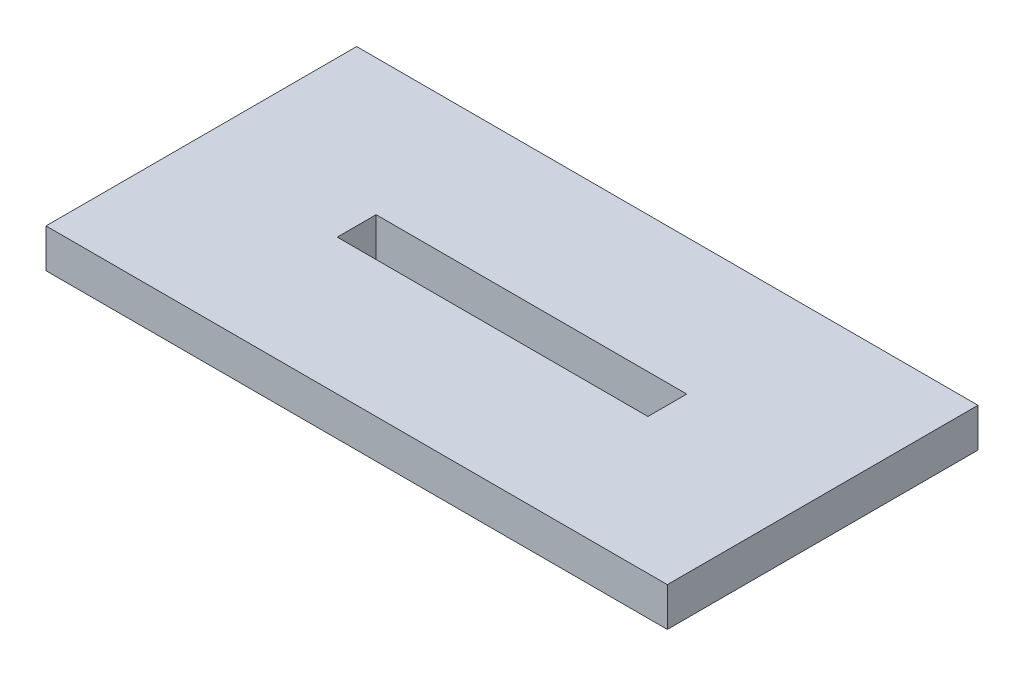
SolidWorks part; units mm, degrees
ref_plane "Front Plane" through (0, 0, 0) normal (0, 0, 1) x (1, 0, 0)
ref_plane "Top Plane" through (0, 0, 0) normal (0, 1, 0) x (1, 0, 0)
ref_plane "Right Plane" through (0, 0, 0) normal (1, 0, 0) x (0, 0, -1)
sketch "Sketch1" plane through (0, 0, 0) normal (0, 1, 0) x (1, 0, 0)
  line L1 (-25.4, -12.7) -> (25.4, -12.7)
  line L2 (-25.4, -12.7) -> (-25.4, 12.7)
  line L3 (-25.4, 12.7) -> (25.4, 12.7)
  line L4 (25.4, -12.7) -> (25.4, 12.7)
  line L5 (-25.4, -12.7) -> (25.4, 12.7) construction
  line L6 (-25.4, 12.7) -> (25.4, -12.7) construction
  line L7 (-12.7, 1.5875) -> (12.7, 1.5875)
  line L8 (-12.7, 1.5875) -> (-12.7, -1.5875)
  line L9 (-12.7, -1.5875) -> (12.7, -1.5875)
  line L10 (12.7, 1.5875) -> (12.7, -1.5875)
  line L11 (-12.7, 1.5875) -> (12.7, -1.5875) construction
  line L12 (-12.7, -1.5875) -> (12.7, 1.5875) construction
  point P0 (0, 0)
  point P6 (0, 0)
  dimension "D1" = 50.8
  dimension "D2" = 25.4
  dimension "D3" = 25.4
  dimension "D4" = 3.175
extrude "Boss-Extrude1" add sketch "Sketch1" along normal blind 3.175
